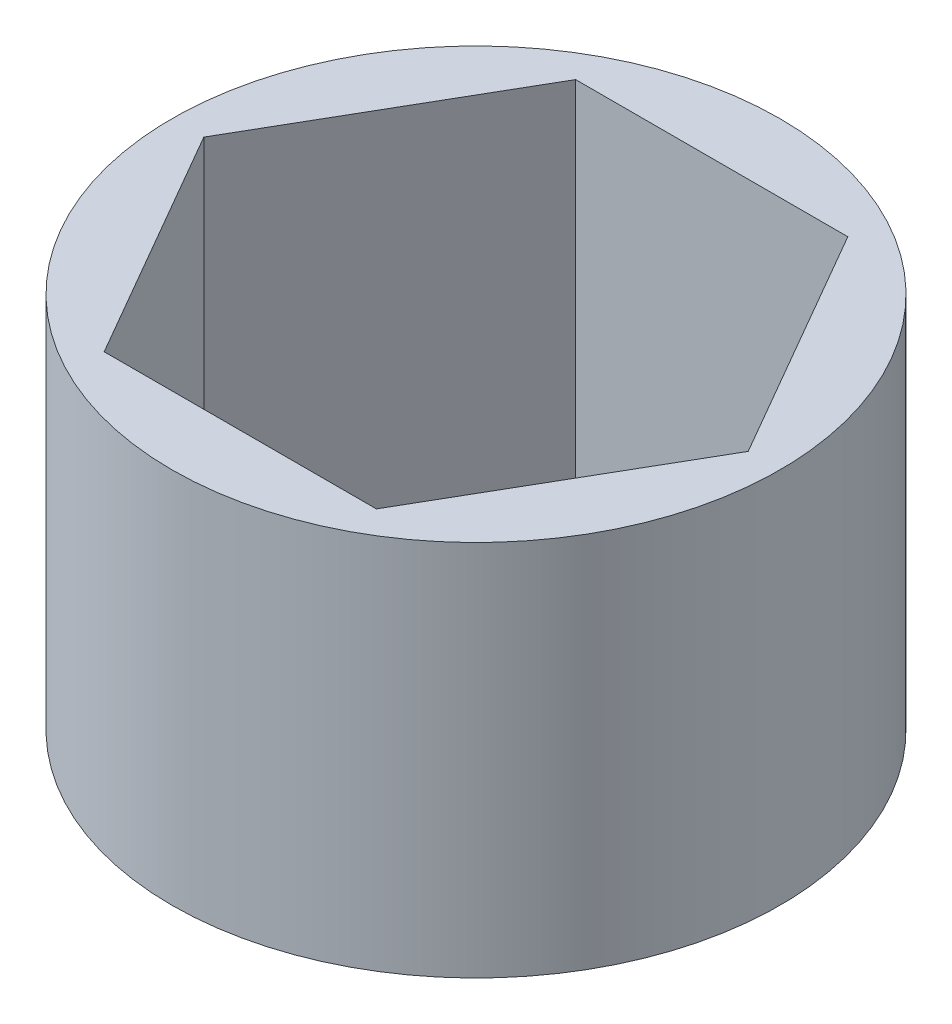
SolidWorks part; units mm, degrees
ref_plane "Front" through (0, 0, 0) normal (0, 0, 1) x (1, 0, 0)
ref_plane "Top" through (0, 0, 0) normal (0, 1, 0) x (1, 0, 0)
ref_plane "Right" through (0, 0, 0) normal (1, 0, 0) x (0, 0, -1)
sketch "Sketch1" plane through (0, 0, 0) normal (0, 1, 0) x (1, 0, 0)
  line L1 (3.6662, 6.35) -> (-3.6662, 6.35)
  line L2 (-3.6662, 6.35) -> (-7.3323, 0)
  line L3 (-7.3323, 0) -> (-3.6662, -6.35)
  line L4 (-3.6662, -6.35) -> (3.6662, -6.35)
  line L5 (3.6662, -6.35) -> (7.3323, 0)
  line L6 (7.3323, 0) -> (3.6662, 6.35)
  circle A0 centre (0, 0) radius 8.1915
  circle A1 centre (0, 0) radius 6.35 construction
  dimension "D2" = 16.383
  dimension "D1" = 12.7
extrude "Boss-Extrude1" add sketch "Sketch1" along normal blind 10.16
